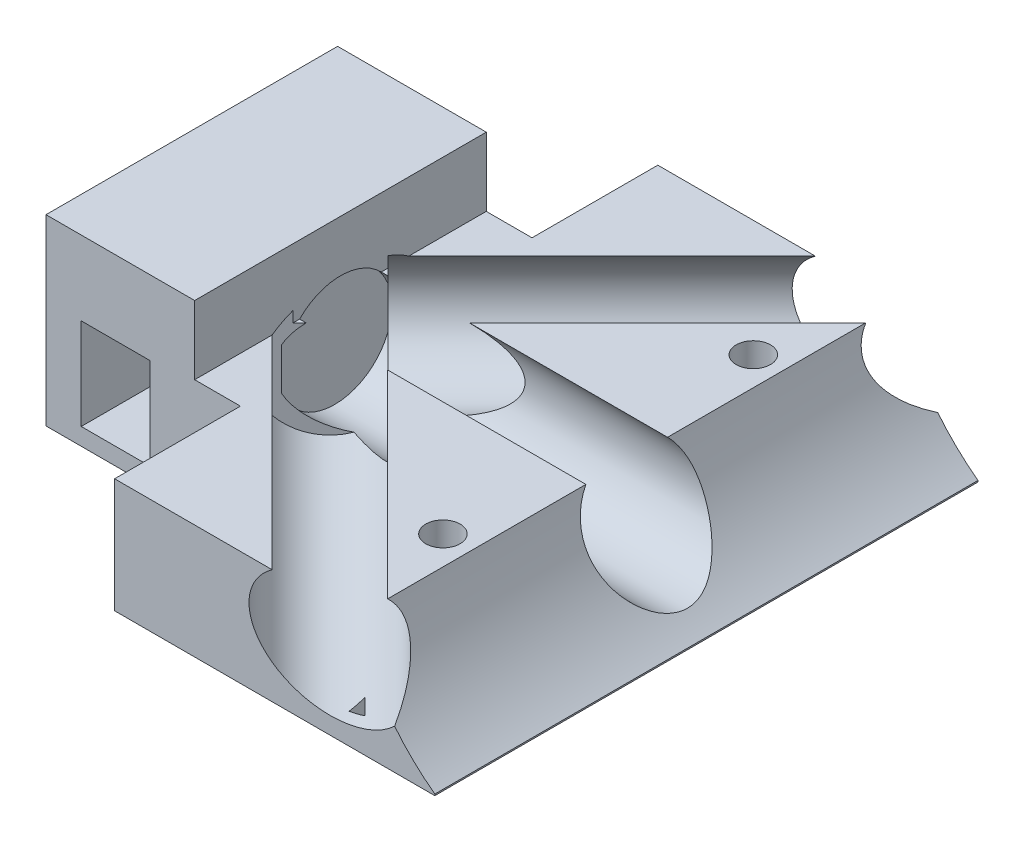
SolidWorks part; units mm, degrees
ref_plane "Front Plane" through (0, 0, 0) normal (0, 0, 1) x (1, 0, 0)
ref_plane "Top Plane" through (0, 0, 0) normal (0, 1, 0) x (1, 0, 0)
ref_plane "Right Plane" through (0, 0, 0) normal (1, 0, 0) x (0, 0, -1)
sketch "Sketch1" plane through (0, 0, 0) normal (0, 1, 0) x (1, 0, 0)
  line L1 (-45, -47.5) -> (45, -47.5)
  line L2 (-45, -47.5) -> (-45, 47.5)
  line L3 (-45, 47.5) -> (45, 47.5)
  line L4 (45, -47.5) -> (45, 47.5)
  line L5 (-45, -47.5) -> (45, 47.5) construction
  line L6 (-45, 47.5) -> (45, -47.5) construction
  point P0 (0, 0)
  dimension "D1" = 95
  dimension "D2" = 90
extrude "Boss-Extrude1" add sketch "Sketch1" along normal blind 20
sketch "Sketch2" plane through (45, 0, 0) normal (1, 0, 0) x (0, 0, -1)
  line L0 (-47.5, 0) -> (47.5, 0) construction
  line L1 (47.5, 20) -> (47.5, 0) construction
  circle A0 centre (0, 13) radius 10
  dimension "D1" = 13
  dimension "D2" = 47.5
extrude "Cut-Extrude2" cut sketch "Sketch2" against normal blind 70
sketch "Sketch3" plane through (0, 0, 47.5) normal (0, 0, 1) x (1, 0, 0)
  line L0 (45, 0) -> (37.4211, 1.8993)
  line L1 (37.4211, 1.8993) -> (30.2523, 20)
  line L2 (-45, 20) -> (45, 20) construction
  line L4 (30.2523, 20) -> (45, 20)
  line L7 (45, 20) -> (45, 0)
extrude "Cut-Extrude3" cut sketch "Sketch3" against normal blind 100
sketch "Sketch5" plane through (0, 0, 47.5) normal (0, 0, 1) x (1, 0, 0)
  line L0 (-45, 0) -> (45, 0) construction
  line L1 (-26.8384, 19) -> (-38.8384, 19)
  line L2 (-26.8384, 19) -> (-26.8384, 3)
  line L3 (-26.8384, 3) -> (-38.8384, 3)
  line L4 (-38.8384, 19) -> (-38.8384, 3)
  dimension "D1" = 12
  dimension "D2" = 3
  dimension "D3" = 16
extrude "Cut-Extrude5" cut sketch "Sketch5" against normal blind 100
fillet "Fillet2" radius 10 1 edges at (37.4211, 1.8993, 0)
sketch "Sketch6" plane through (0, 20, 0) normal (0, 1, 0) x (1, 0, 0)
  line L0 (30.2523, 47.5) -> (-45, 47.5) construction
  line L1 (-45, -47.5) -> (-21, -47.5)
  line L2 (-45, -47.5) -> (-45, 47.5)
  line L3 (-45, 47.5) -> (-21, 47.5)
  line L4 (-21, -47.5) -> (-21, 47.5)
  dimension "D1" = 24
extrude "Boss-Extrude2" add sketch "Sketch6" along normal blind 24
sketch "Sketch7" plane through (0, 20, 0) normal (0, 1, 0) x (1, 0, 0)
  line L0 (-21, -47.5) -> (30.2523, -47.5) construction
  line L1 (-19, -45.5) -> (28.2523, -45.5)
  line L2 (-19, -45.5) -> (-19, -11.5014)
  line L3 (-19, -11.5014) -> (28.2523, -11.5014)
  line L4 (28.2523, -45.5) -> (28.2523, -11.5014)
  line L5 (30.2523, -7.1414) -> (-21, -7.1414) construction
  line L6 (-21, -47.5) -> (-21, -7.1414) construction
  line L7 (30.2523, -7.1414) -> (30.2523, -47.5) construction
  dimension "D1" = 2
  dimension "D2" = 4.36
  dimension "D3" = 2
  dimension "D4" = 2
  dimension "D5" = 33.9986
extrude "Cut-Extrude7" cut sketch "Sketch7" against normal blind 17
sketch "Sketch8" plane through (0, 20, 0) normal (0, 1, 0) x (1, 0, 0)
  line L0 (30.2523, 47.5) -> (-21, 47.5) construction
  line L1 (-19, 11.5) -> (28.2523, 11.5)
  line L2 (-19, 11.5) -> (-19, 45.5)
  line L3 (-19, 45.5) -> (28.2523, 45.5)
  line L4 (28.2523, 11.5) -> (28.2523, 45.5)
  line L5 (30.2523, 47.5) -> (30.2523, 7.1414) construction
  line L6 (-21, 7.1414) -> (-21, 47.5) construction
  dimension "D1" = 2
  dimension "D2" = 34
  dimension "D3" = 2
  dimension "D4" = 2
extrude "Cut-Extrude8" cut sketch "Sketch8" against normal blind 17
sketch "Sketch10" plane through (-21, 0, 0) normal (1, 0, 0) x (0, 0, -1)
  line L1 (-47.5, 44) -> (47.5, 44)
  line L2 (-47.5, 44) -> (-47.5, 20)
  line L3 (-47.5, 20) -> (47.5, 20)
  line L4 (47.5, 44) -> (47.5, 20)
extrude "Boss-Extrude3" add sketch "Sketch10" along normal blind 25
sketch "Sketch12" plane through (-45, 0, 0) normal (-1, 0, 0) x (0, 0, 1)
  line L1 (47.5, 0) -> (25.5, 0)
  line L2 (47.5, 0) -> (47.5, 32)
  line L3 (47.5, 32) -> (25.5, 32)
  line L4 (25.5, 0) -> (25.5, 32)
  dimension "D1" = 32
  dimension "D2" = 22
extrude "Cut-Extrude9" cut sketch "Sketch12" against normal blind 34
sketch "Sketch13" plane through (-45, 0, 0) normal (-1, 0, 0) x (0, 0, 1)
  line L1 (-47.5, 0) -> (-25.5, 0)
  line L2 (-47.5, 0) -> (-47.5, 32)
  line L3 (-47.5, 32) -> (-25.5, 32)
  line L4 (-25.5, 0) -> (-25.5, 32)
  dimension "D1" = 22
  dimension "D2" = 32
extrude "Cut-Extrude10" cut sketch "Sketch13" against normal blind 34
sketch "Sketch14" plane through (0, 0, -47.5) normal (0, 0, -1) x (-1, 0, 0)
  line L0 (11, 32) -> (45, 32) construction
  circle A0 centre (31.5228, 44) radius 10
  dimension "D1" = 12
extrude "Cut-Extrude11" cut sketch "Sketch14" against normal blind 100
sketch "Sketch18" plane through (0, 0, -47.5) normal (0, 0, -1) x (-1, 0, 0)
  line L0 (11, 32) -> (45, 32) construction
  line L1 (-4, 44) -> (15.5228, 44)
  line L2 (-4, 44) -> (-4, 32)
  line L3 (-4, 32) -> (15.5228, 32)
  line L4 (15.5228, 44) -> (15.5228, 32)
  dimension "D1" = 6
extrude "Cut-Extrude13" cut sketch "Sketch18" against normal blind 100
sketch "Sketch19" plane through (-25, 0, 0) normal (1, 0, 0) x (0, 0, -1)
  circle A0 centre (0, 13) radius 10
  arc A1 (-7.1414, 20) -> (7.1414, 20) centre (0, 13) ccw construction
  dimension "D1" = 0
extrude "Boss-Extrude5" add sketch "Sketch19" along normal blind 60
sketch "Sketch20" plane through (0, 0, 47.5) normal (0, 0, 1) x (1, 0, 0)
  line L1 (30.2523, 20) -> (45, 20)
  line L2 (30.2523, 20) -> (30.2523, 0)
  line L3 (30.2523, 0) -> (45, 0)
  line L4 (45, 20) -> (45, 0)
extrude "Boss-Extrude6" add sketch "Sketch20" against normal blind 95
sketch "Sketch21" plane through (0, 20, 0) normal (0, 1, 0) x (1, 0, 0)
  line L1 (45, -47.5) -> (4, -47.5)
  line L2 (45, -47.5) -> (45, 47.5)
  line L3 (45, 47.5) -> (4, 47.5)
  line L4 (4, -47.5) -> (4, 47.5)
extrude "Cut-Extrude16" cut sketch "Sketch21" along normal blind 17
sketch "Sketch23" plane through (0, 0, 47.5) normal (0, 0, 1) x (1, 0, 0)
  line L1 (-11, 32) -> (4, 32)
  line L2 (-11, 32) -> (-11, 20)
  line L3 (-11, 20) -> (4, 20)
  line L4 (4, 32) -> (4, 20)
extrude "Cut-Extrude17" cut sketch "Sketch23" against normal blind 100
sketch "Sketch29" plane through (0, 0, 47.5) normal (0, 0, 1) x (1, 0, 0)
  line L1 (-45, 32) -> (-3.6177, 32)
  line L2 (-45, 32) -> (-45, 73.2631)
  line L3 (-45, 73.2631) -> (-3.6177, 73.2631)
  line L4 (-3.6177, 32) -> (-3.6177, 73.2631)
extrude "Cut-Extrude22" cut sketch "Sketch29" against normal blind 100
sketch "Sketch30" plane through (0, 0, 25.5) normal (0, 0, 1) x (1, 0, 0)
  line L1 (-11, 32) -> (-19, 32)
  line L2 (-11, 32) -> (-11, 20)
  line L3 (-11, 20) -> (-19, 20)
  line L4 (-19, 32) -> (-19, 20)
extrude "Cut-Extrude23" cut sketch "Sketch30" against normal blind 100
sketch "Sketch31" plane through (0, 20, 0) normal (0, 1, 0) x (1, 0, 0)
  line L1 (-19, -11.5014) -> (28.2523, -11.5014)
  line L2 (-19, -11.5014) -> (-19, 11.5)
  line L3 (-19, 11.5) -> (28.2523, 11.5)
  line L4 (28.2523, -11.5014) -> (28.2523, 11.5)
extrude "Cut-Extrude24" cut sketch "Sketch31" against normal blind 17
sketch "Sketch33" plane through (0, 3, 0) normal (0, 1, 0) x (1, 0, 0)
  line L1 (-11, -45.5) -> (28.2523, -45.5)
  line L2 (-11, -45.5) -> (-11, 45.5)
  line L3 (-11, 45.5) -> (28.2523, 45.5)
  line L4 (28.2523, -45.5) -> (28.2523, 45.5)
extrude "Boss-Extrude7" add sketch "Sketch33" along normal blind 17
sketch "Sketch34" plane through (0, 3, 0) normal (0, 1, 0) x (1, 0, 0)
  line L0 (-19, -25.5) -> (-11, -25.5) construction
  line L1 (-11, 25.5) -> (-19, 25.5)
  line L2 (-11, 25.5) -> (-11, -25.5)
  line L3 (-11, -25.5) -> (-19, -25.5)
  line L4 (-19, 25.5) -> (-19, -25.5)
extrude "Boss-Extrude8" add sketch "Sketch34" along normal blind 17
sketch "Sketch35" plane through (0, 20, 0) normal (0, 1, 0) x (1, 0, 0)
  line L0 (45, -64.5) -> (62, -47.5)
  line L1 (45, -47.5) -> (62, -47.5)
  line L2 (45, -47.5) -> (45, -64.5)
  dimension "D1" = 17
  dimension "D2" = 17
extrude "Boss-Extrude10" add sketch "Sketch35" against normal blind 20 separate body
sketch "Sketch36" plane through (0, 20, 0) normal (0, 1, 0) x (1, 0, 0)
  line L0 (62, 47.5) -> (45, 64.5)
  line L1 (45, 47.5) -> (62, 47.5)
  line L2 (45, 47.5) -> (45, 64.5)
  dimension "D1" = 17
  dimension "D2" = 17
extrude "Boss-Extrude13" add sketch "Sketch36" against normal blind 20 separate body contours L0 L2 L1
sketch "Sketch43" plane through (54.75, 0, 54.75) normal (0.7071, 0, 0.7071) x (0.7071, 0, -0.7071)
  line L0 (-13.7886, 0) -> (10.253, 0) construction
  line L1 (10.253, 0) -> (10.253, 20) construction
  circle A0 centre (-14.747, 13) radius 10
  point P6 (0.3874, 14.5685)
  dimension "D1" = 13
  dimension "D2" = 25
extrude "Cut-Extrude35" cut sketch "Sketch43" against normal blind 85
sketch "Sketch44" plane through (54.75, 0, -54.75) normal (0.7071, 0, -0.7071) x (-0.7071, 0, -0.7071)
  line L0 (-10.253, 0) -> (13.7886, 0) construction
  line L1 (-10.253, 0) -> (-10.253, 20) construction
  circle A0 centre (14.747, 13) radius 10
  dimension "D1" = 13
  dimension "D2" = 25
extrude "Cut-Extrude36" cut sketch "Sketch44" against normal blind 85
sketch "Sketch45" plane through (0, 20, 0) normal (0, 1, 0) x (1, 0, 0)
  line L1 (45, -47.5) -> (70.4011, -47.5)
  line L2 (45, -47.5) -> (45, -70.3456)
  line L3 (45, -70.3456) -> (70.4011, -70.3456)
  line L4 (70.4011, -47.5) -> (70.4011, -70.3456)
extrude "Cut-Extrude37" cut sketch "Sketch45" against normal blind 85
sketch "Sketch46" plane through (0, 20, 0) normal (0, 1, 0) x (1, 0, 0)
  line L1 (45, 47.5) -> (66.6361, 47.5)
  line L2 (45, 47.5) -> (45, 69.6416)
  line L3 (45, 69.6416) -> (66.6361, 69.6416)
  line L4 (66.6361, 47.5) -> (66.6361, 69.6416)
extrude "Cut-Extrude38" cut sketch "Sketch46" against normal blind 85
sketch "Sketch48" plane through (45, 0, 0) normal (1, 0, 0) x (0, 0, -1)
  line L0 (-47.5, 0) -> (47.5, 0) construction
  line L1 (47.5, 0) -> (47.5, 20) construction
  circle A0 centre (0, 13) radius 10
  point P6 (45.8322, 9.3624)
  point P9 (29.0112, 15.1457)
  dimension "D1" = 13
  dimension "D2" = 47.5
extrude "Cut-Extrude40" cut sketch "Sketch48" against normal blind 65
sketch "Sketch49" plane through (0, 0, -47.5) normal (0, 0, -1) x (-1, 0, 0)
  circle A0 centre (-68.1577, 31.3858) radius 38.8043
extrude "Cut-Extrude41" cut sketch "Sketch49" against normal blind 100
sketch "Sketch50" plane through (0, 0, 0) normal (0, -1, 0) x (-1, 0, 0)
  line L0 (11, -47.5) -> (-45, -47.5) construction
  line L1 (-38, -45.5) -> (-28, -45.5)
  line L2 (-38, -45.5) -> (-38, -28.5)
  line L3 (-38, -28.5) -> (-28, -28.5)
  line L4 (-28, -45.5) -> (-28, -28.5)
  line L5 (-45, -47.5) -> (-45, 47.5) construction
  point P8 (-40.8527, -35.877)
  dimension "D1" = 17
  dimension "D2" = 10
  dimension "D3" = 2
  dimension "D4" = 7
extrude "Cut-Extrude43" cut sketch "Sketch50" against normal blind 4
sketch "Sketch51" plane through (0, 0, 0) normal (0, -1, 0) x (-1, 0, 0)
  line L0 (-45, -47.5) -> (-45, 47.5) construction
  line L1 (-38, 28.5) -> (-28, 28.5)
  line L2 (-38, 28.5) -> (-38, 45.5)
  line L3 (-38, 45.5) -> (-28, 45.5)
  line L4 (-28, 28.5) -> (-28, 45.5)
  line L5 (-45, 47.5) -> (11, 47.5) construction
  point P8 (-38.434, 47.5)
  dimension "D1" = 17
  dimension "D2" = 10
  dimension "D3" = 7
  dimension "D4" = 2
extrude "Cut-Extrude44" cut sketch "Sketch51" against normal blind 4
sketch "Sketch52" plane through (0, 20, 0) normal (0, 1, 0) x (1, 0, 0)
  line L0 (31.0614, -7.1414) -> (-3.6144, -7.1414) construction
  line L1 (31.0614, -41.8172) -> (31.0614, -7.1414) construction
  circle A0 centre (26.0614, -27.1414) radius 3
  point P6 (-50.5523, -60.3116)
  dimension "D1" = 20
  dimension "D2" = 5
extrude "Cut-Extrude45" cut sketch "Sketch52" against normal blind 100
sketch "Sketch53" plane through (0, 20, 0) normal (0, 1, 0) x (1, 0, 0)
  line L0 (-3.6144, 7.1414) -> (31.0614, 7.1414) construction
  line L1 (31.0614, 7.1414) -> (31.0614, 41.8172) construction
  circle A0 centre (26.0614, 27.1414) radius 3
  dimension "D1" = 20
  dimension "D2" = 5
extrude "Cut-Extrude46" cut sketch "Sketch53" against normal blind 100
